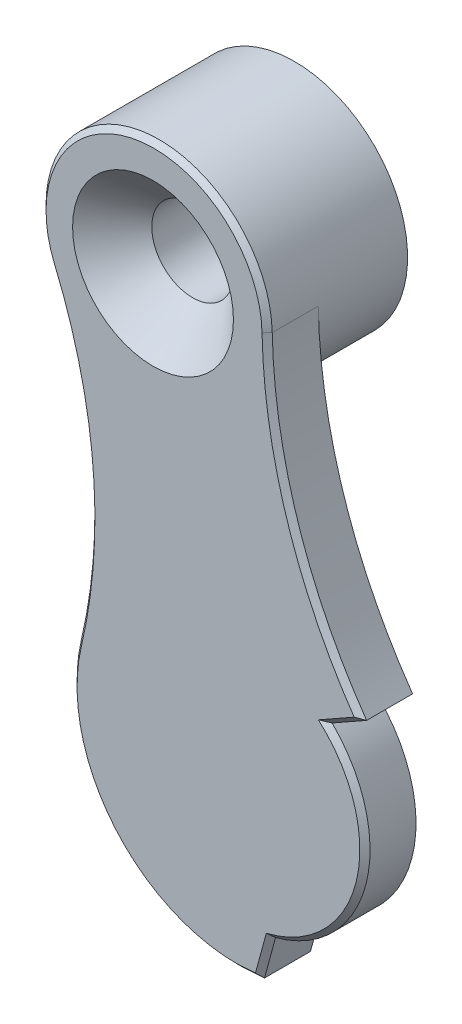
SolidWorks part; units mm, degrees
ref_plane "前视基准面" through (0, 0, 0) normal (0, 0, 1) x (1, 0, 0)
ref_plane "上视基准面" through (0, 0, 0) normal (0, 1, 0) x (1, 0, 0)
ref_plane "右视基准面" through (0, 0, 0) normal (1, 0, 0) x (0, 0, -1)
ref_plane "基准面4" through (0, 0, 12.16) normal (0, 0, -1) x (-1, 0, 0)
sketch "草图1" plane through (0, 0, 12.16) normal (0, 0, -1) x (-1, 0, 0)
  line L0 (10.9008, -4.8283) -> (11.334, -6.4163)
  line L2 (-0.0012, 0) -> (49999.9988, 0) construction
  line L3 (12.2, -6.475) -> (11.334, -6.4163)
  line L4 (8.6859, 3.5568) -> (7.3341, 4.321)
  line L8 (5.1456, 5.5218) -> (7.3149, 4.3316) construction
  arc A0 (8.6859, 3.5568) -> (10.9008, -4.8283) centre (12.2, 0) ccw
  arc A1 (12.2, -6.475) -> (18.5038, 1.4793) centre (12.2, 0) ccw
  arc A2 (19.5429, 13.8116) -> (18.5038, 1.4793) centre (37.9748, 6.0486) ccw
  arc A3 (19.5429, 13.8116) -> (11.0312, 15.6241) centre (15.4602, 15.5311) ccw
  arc A4 (11.0312, 15.6241) -> (7.3341, 4.321) centre (-9.407, 16.053) cw
  dimension "D3" = 4.43
  dimension "D2" = 20
  dimension "D6" = 12.95
  dimension "D7" = 5
extrude "凸台-拉伸1" add sketch "草图1" against normal blind 2
sketch "草图2" plane through (0, 0, 12.16) normal (0, 0, -1) x (-1, 0, 0)
  circle A5 centre (15.4602, 15.5311) radius 4.43
extrude "凸台-拉伸2" add sketch "草图2" along normal blind 3.5
hole_wizard "M3 平头机械螺钉的锥形沉头孔1" positions "草图7" profile "草图6" countersink size "M3" standard "Ansi Metric" end condition through all
sketch "草图7" plane through (0, 0, 14.16) normal (0, 0, 1) x (1, 0, 0)
  point P0 (-15.5, 15.5)
sketch "草图6" plane through (-15.5, 15.5, 14.16) normal (1, 0, 0) x (0, -1, 0)
  line L0 (0, 0) -> (0, 5.5)
  line L1 (0, 5.5) -> (1.6, 5.5)
  line L2 (1.6, 5.5) -> (1.6, 1.55)
  line L3 (1.6, 1.55) -> (3.15, 0)
  line L5 (3.15, 0) -> (0, 0)
  line L6 (-1.6, 1.55) -> (-3.15, 0) construction
  line L11 (0, -6.35) -> (0, 107.95) construction
  dimension "通孔孔直径" = 3.2
  dimension "通孔孔深度" = 5.5
  dimension "近端锥形沉头孔直径" = 6.3
  dimension "近端锥形沉头孔角度" = 90
sketch "草图8" plane through (0, 0, 12.16) normal (0, 0, -1) x (-1, 0, 0)
  line L0 (0, 0) -> (-50000, 0) construction
  circle A0 centre (12.24, 0) radius 3
  dimension "D1" = 12.24
extrude "凸台-拉伸3" add sketch "草图8" along normal blind 0.9
sketch "草图10" plane through (0, 0, 11.26) normal (0, 0, 1) x (1, 0, 0)
  line L0 (0, 0) -> (-50000, 0) construction
  circle A0 centre (-12.2, 0) radius 1.52
extrude "切除-拉伸1" cut sketch "草图10" along normal blind 2
chamfer "倒角1" distance 0.2 angle 45 8 edges at (-16.3828, 19.864, 14.16) (-10.0227, 9.6978, 14.16) (-8.01, 3.9389, 14.16) (-7.3658, -1.277, 14.16) (-11.1174, -5.6223, 14.16) (-11.767, -6.4457, 14.16) (-17.2747, -4.0216, 14.16) (-18.0454, 7.7279, 14.16)
